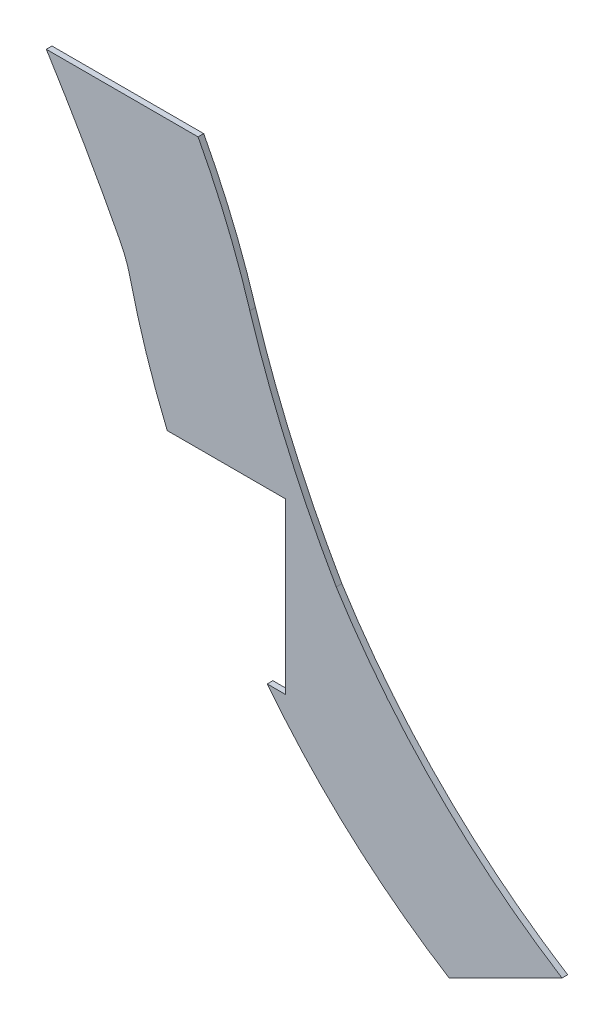
SolidWorks part; units mm, degrees
ref_plane "Alzado" through (0, 0, 0) normal (0, 0, 1) x (1, 0, 0)
ref_plane "Planta" through (0, 0, 0) normal (0, 1, 0) x (1, 0, 0)
ref_plane "Vista lateral" through (0, 0, 0) normal (1, 0, 0) x (0, 0, -1)
sketch "Model" plane through (0, 0, 0) normal (0, 0, 1) x (1, 0, 0)
  line L0 (34.6494, 11.961) -> (32.6494, 10.961)
  line L1 (29.7506, 16.861) -> (29.7506, 13.861)
  line L2 (27.6581, 16.861) -> (29.7506, 16.861)
  line L3 (29.7506, 13.861) -> (29.4288, 13.861)
  line L4 (25.5166, 21.639) -> (28.2039, 21.639)
  arc A0 (26.9993, 18.8824) -> (27.6581, 16.861) centre (39.5396, 21.8512) ccw
  arc A1 (26.9993, 18.8824) -> (26.8266, 19.3462) centre (25.0531, 18.4216) ccw
  arc A2 (26.8266, 19.3462) -> (25.5166, 21.639) centre (-3.5935, 3.487) ccw
  arc A3 (29.1211, 19.4308) -> (28.2039, 21.639) centre (17.0688, 15.7195) ccw
  arc A4 (29.1211, 19.4308) -> (30.6506, 15.959) centre (45.9274, 24.7621) ccw
  arc A5 (30.6506, 15.959) -> (34.6494, 11.961) centre (41.4999, 22.8115) ccw
  arc A6 (29.4288, 13.861) -> (32.6494, 10.961) centre (39.294, 21.5785) ccw
extrude "Saliente-Extruir1" add sketch "Model" along normal blind 0.1
